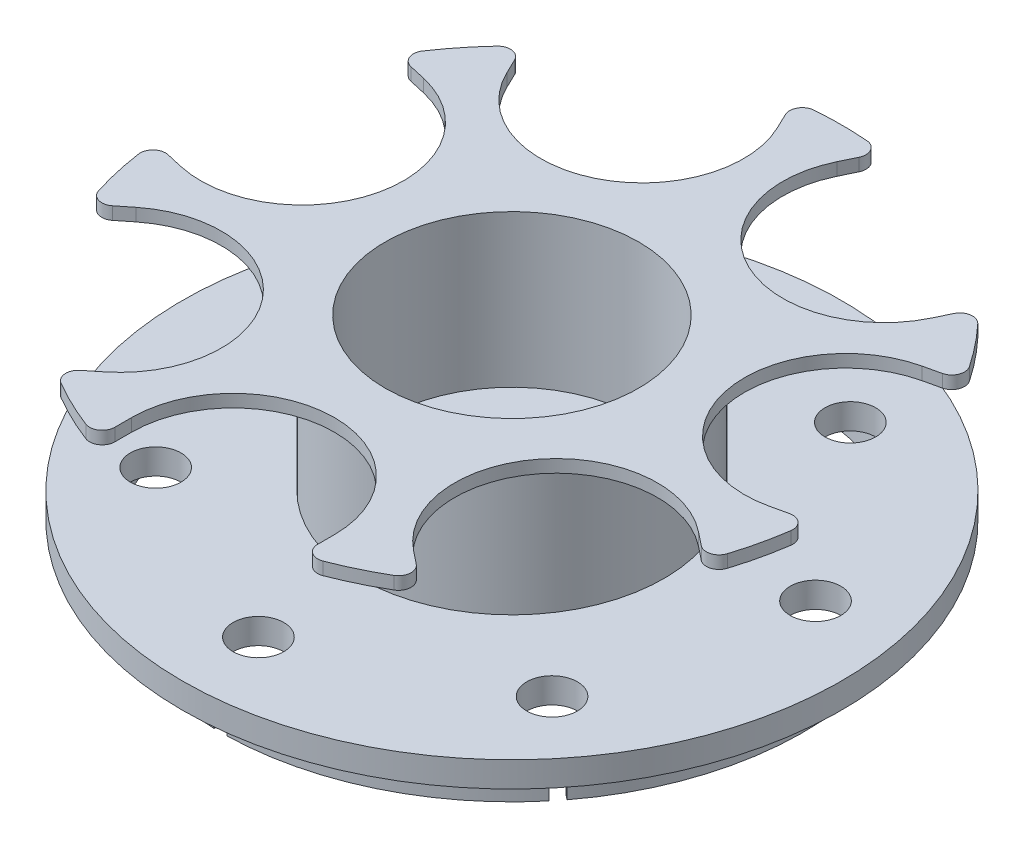
SolidWorks part; units mm, degrees
material "ABS"
ref_plane "Front Plane" through (0, 0, 0) normal (0, 0, 1) x (1, 0, 0)
ref_plane "Top Plane" through (0, 0, 0) normal (0, 1, 0) x (1, 0, 0)
ref_plane "Right Plane" through (0, 0, 0) normal (1, 0, 0) x (0, 0, -1)
sketch "Sketch1" plane through (0, 0, 0) normal (0, 1, 0) x (1, 0, 0)
  circle A0 centre (0, 0) radius 130
extrude "Boss-Extrude1" add sketch "Sketch1" along normal blind 10
sketch "Sketch2" plane through (0, 10, 0) normal (0, 1, 0) x (1, 0, 0)
  circle A0 centre (0, 0) radius 35
extrude "Cut-Extrude1" cut sketch "Sketch2" against normal up to next
sketch "Sketch3" plane through (0, 10, 0) normal (0, 1, 0) x (1, 0, 0)
  circle A0 centre (0, 0) radius 50
  circle A1 centre (0, 0) radius 60
extrude "Boss-Extrude2" add sketch "Sketch3" along normal blind 55
sketch "Sketch4" plane through (0, 65, 0) normal (0, 1, 0) x (1, 0, 0)
  circle A0 centre (0, 0) radius 50
  circle A1 centre (0, 0) radius 130
extrude "Boss-Extrude3" add sketch "Sketch4" along normal blind 5
sketch "Sketch6" plane through (0, 0, 0) normal (0, -1, 0) x (1, 0, 0)
  circle A0 centre (0, 0) radius 45
  circle A1 centre (0, 0) radius 60
extrude "Boss-Extrude4" add sketch "Sketch6" along normal blind 15
sketch "Sketch8" plane through (0, 70, 0) normal (0, 1, 0) x (1, 0, 0)
  line L2 (40, -110) -> (40, -123.6932)
  line L4 (-40, -110) -> (-40, -123.6932)
  line L5 (40, -110) -> (-40, -150) construction
  line L6 (40, -150) -> (-40, -110) construction
  circle A0 centre (0, 0) radius 130 construction
  arc A1 (-40, -110) -> (40, -110) centre (0, -110) cw
  arc A2 (-40, -123.6932) -> (40, -123.6932) centre (0, 0) ccw
  point P0 (0, -130)
extrude "Cut-Extrude3" cut sketch "Sketch8" against normal up to next (5 mm away)
pattern_circular "CirPattern1" count 7 over 360 about axis through (0, 0, 0) along (0, 1, 0) of "Cut-Extrude3"
sketch "Sketch10" plane through (0, 0, 0) normal (0, -1, 0) x (1, 0, 0)
  circle A0 centre (0, 0) radius 115
  circle A1 centre (0, 0) radius 112
extrude "Boss-Extrude5" add sketch "Sketch10" along normal blind 15
sketch "Sketch11" plane through (0, -15, 0) normal (0, -1, 0) x (1, 0, 0)
  line L1 (-2.5, 122.5) -> (2.5, 122.5)
  line L2 (-2.5, 122.5) -> (-2.5, 97.5)
  line L3 (-2.5, 97.5) -> (2.5, 97.5)
  line L4 (2.5, 122.5) -> (2.5, 97.5)
  line L5 (-2.5, 122.5) -> (2.5, 97.5) construction
  line L6 (-2.5, 97.5) -> (2.5, 122.5) construction
  point P0 (0, 110)
extrude "Cut-Extrude4" cut sketch "Sketch11" against normal up to surface (15 mm away) up to face at (0, 0, 115)
pattern_circular "CirPattern2" count 7 over 360 about axis through (0, 0, 0) along (0, 1, 0) of "Cut-Extrude4"
sketch "Sketch12" plane through (0, 10, 0) normal (0, 1, 0) x (1, 0, 0)
  circle A0 centre (0, -100) radius 10
  dimension "D1" = 100
extrude "Cut-Extrude5" cut sketch "Sketch12" against normal up to next (10 mm away)
pattern_circular "CirPattern3" count 7 over 360 about axis through (0, 0, 0) along (0, 1, 0) of "Cut-Extrude5"
fillet "Fillet1" radius 5 14 edges at (-129.4928, 67.5, 11.4728) (-121.6468, 67.5, 45.8482) (-111.6911, 67.5, -66.5214) (-89.7072, 67.5, -94.0883) (-17.6297, 67.5, -128.799) (17.6297, 67.5, -128.799) (89.7072, 67.5, -94.0883) (111.6911, 67.5, -66.5214) (129.4928, 67.5, 11.4728) (121.6468, 67.5, 45.8482) (71.7676, 67.5, 108.3947) (40, 67.5, 123.6932) (-71.7676, 67.5, 108.3947) (-40, 67.5, 123.6932)
